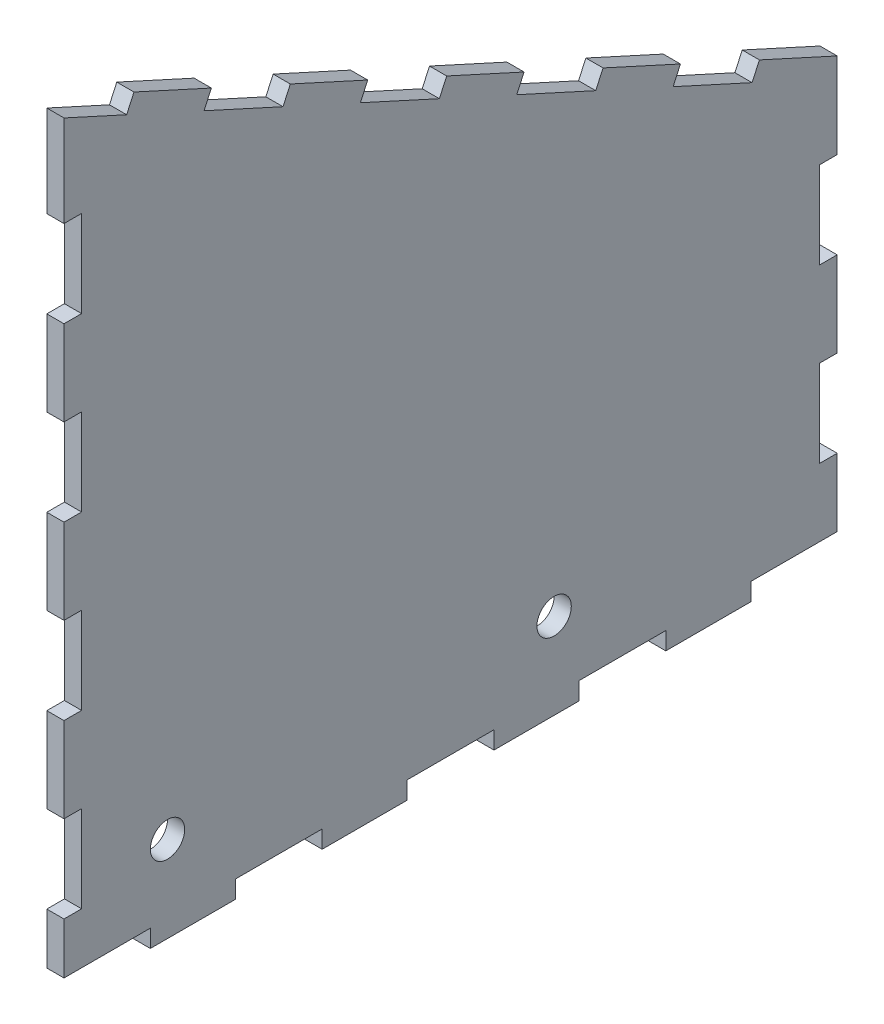
SolidWorks part; units mm, degrees
ref_plane "Front Plane" through (0, 0, 0) normal (0, 0, 1) x (1, 0, 0)
ref_plane "Top Plane" through (0, 0, 0) normal (0, 1, 0) x (1, 0, 0)
ref_plane "Right Plane" through (0, 0, 0) normal (1, 0, 0) x (0, 0, -1)
sketch "Sketch1" plane through (0, 0, 0) normal (1, 0, 0) x (0, 0, -1)
  line L1 (-60.1559, 92) -> (119.8441, 10)
  line L2 (-60.1559, 92) -> (-60.1559, -90)
  line L3 (-60.1559, -90) -> (119.8441, -90)
  line L4 (119.8441, 10) -> (119.8441, -90)
  line L5 (-60.1559, 92) -> (119.8441, -90) construction
  line L6 (-60.1559, -90) -> (119.8441, 10) construction
  point P0 (-0.1559, 0)
  dimension "D1" = 182
  dimension "D2" = 180
  dimension "D3" = 100
  dimension "D4" = 90
  dimension "D5" = 120
extrude "Boss-Extrude1" add sketch "Sketch1" along normal blind 4
sketch "Sketch2" plane through (4, 0, 0) normal (1, 0, 0) x (0, 0, -1)
  line L0 (-60.1559, -90) -> (119.8441, -90) construction
  line L1 (-40.0559, -90) -> (-60.2559, -90)
  line L2 (-40.0559, -90) -> (-40.0559, -85.9)
  line L3 (-40.0559, -85.9) -> (-60.2559, -85.9)
  line L4 (-60.2559, -90) -> (-60.2559, -85.9)
  line L6 (-60.1559, 92) -> (-60.1559, -90) construction
  dimension "D1" = 20.2
  dimension "D2" = 4.1
  dimension "D3" = 0.1
extrude "Cut-Extrude1" cut sketch "Sketch2" against normal through all
pattern_linear "LPattern1" count 6 spacing 40 along (0, 0, -1) of "Cut-Extrude1"
sketch "Sketch3" plane through (4, 0, 0) normal (1, 0, 0) x (0, 0, -1)
  line L0 (-60.1559, 92) -> (-60.1559, -85.9) construction
  line L1 (-60.1559, -53.8) -> (-56.0559, -53.8)
  line L2 (-60.1559, -53.8) -> (-60.1559, -74)
  line L3 (-60.1559, -74) -> (-56.0559, -74)
  line L4 (-56.0559, -53.8) -> (-56.0559, -74)
  line L5 (-40.0559, -85.9) -> (-60.1559, -85.9) construction
  dimension "D1" = 4.1
  dimension "D2" = 20.2
  dimension "D3" = 11.9
extrude "Cut-Extrude2" cut sketch "Sketch3" against normal blind 4
pattern_linear "LPattern2" count 4 spacing 40 along (0, 1, 0) of "Cut-Extrude2"
sketch "Sketch4" plane through (4, 0, 0) normal (1, 0, 0) x (0, 0, -1)
  line L0 (119.8441, -85.9) -> (119.8441, 10) construction
  line L1 (119.8441, -70.1) -> (115.7441, -70.1)
  line L2 (119.8441, -70.1) -> (119.8441, -49.9)
  line L3 (119.8441, -49.9) -> (115.7441, -49.9)
  line L4 (115.7441, -70.1) -> (115.7441, -49.9)
  line L6 (79.9441, -90) -> (99.7441, -90) construction
  dimension "D1" = 4.1
  dimension "D2" = 20.2
  dimension "D3" = 19.9
extrude "Cut-Extrude3" cut sketch "Sketch4" against normal blind 4
pattern_linear "LPattern3" count 2 spacing 40 along (0, 1, 0) of "Cut-Extrude3"
sketch "Sketch5" plane through (4, 0, 0) normal (1, 0, 0) x (0, 0, -1)
  line L0 (101.7347, 18.2498) -> (83.3523, 26.624)
  line L1 (101.7347, 18.2498) -> (100.035, 14.5188)
  line L2 (83.3523, 26.624) -> (81.6526, 22.893)
  line L3 (100.035, 14.5188) -> (81.6526, 22.893)
  line L4 (119.8441, 10) -> (-60.1559, 92) construction
  dimension "D1" = 20.2
  dimension "D2" = 4.1
  dimension "D3" = 19.9
extrude "Cut-Extrude4" cut sketch "Sketch5" against normal blind 4
pattern_linear "LPattern4" count 6 spacing 40 along (0, 0.4146, 0.91) of "Cut-Extrude4"
sketch "Sketch6" plane through (4, 0, 0) normal (1, 0, 0) x (0, 0, -1)
  line L0 (-56.0559, -74) -> (-56.0559, -53.8) construction
  line L1 (-40.0559, -90) -> (-20.2559, -90) construction
  line L2 (39.9441, -90) -> (59.7441, -90) construction
  circle A0 centre (-36.0559, -70) radius 4
  circle A1 centre (53.9441, -70) radius 4
  point P6 (-56.0559, -63.9)
  dimension "D3" = 8
  dimension "D4" = 8
  dimension "D1" = 110
  dimension "D2" = 20
  dimension "D5" = 20
  dimension "D6" = 20
extrude "Cut-Extrude5" cut sketch "Sketch6" against normal through all
